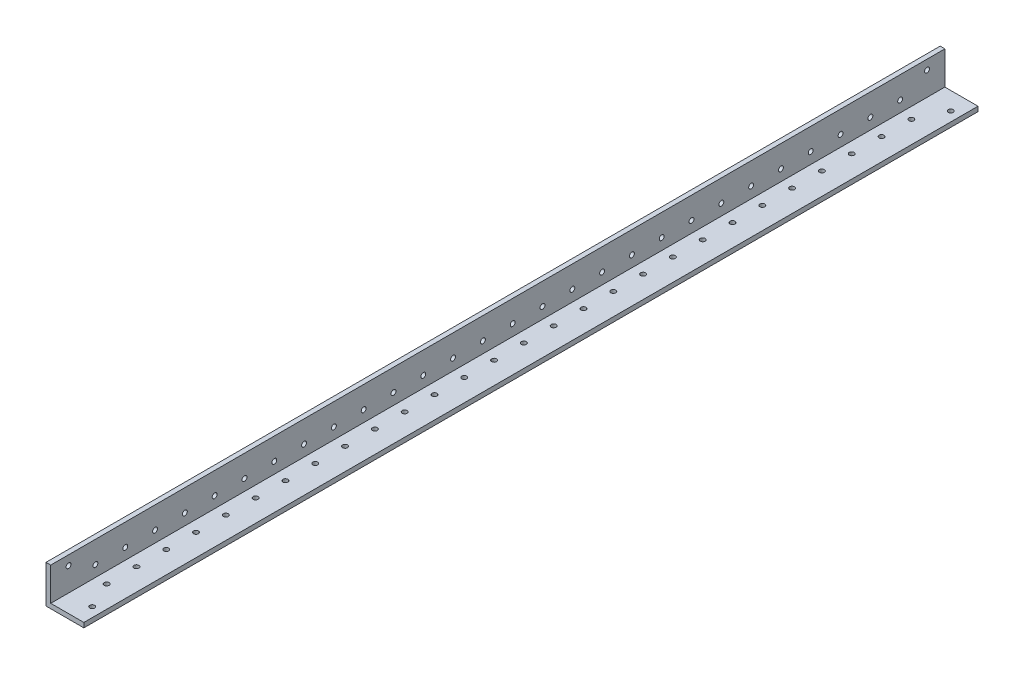
SolidWorks part; units mm, degrees
material "6061-T6 (SS)"
ref_plane "Front Plane" through (0, 0, 0) normal (0, 0, 1) x (1, 0, 0)
ref_plane "Top Plane" through (0, 0, 0) normal (0, 1, 0) x (1, 0, 0)
ref_plane "Right Plane" through (0, 0, 0) normal (1, 0, 0) x (0, 0, -1)
sketch "Sketch1" plane through (0, 0, 0) normal (0, 0, 1) x (1, 0, 0)
  line L0 (0, 25.4) -> (0, 0) construction
  line L1 (0, 0) -> (25.4, 0) construction
  line L2 (25.4, 0) -> (25.4, 3.175) construction
  line L3 (25.4, 3.175) -> (3.175, 3.175) construction
  line L4 (3.175, 3.175) -> (3.175, 25.4) construction
  line L6 (3.175, 25.4) -> (0, 25.4) construction
  arc A0 (3.175, 3.5814) -> (3.5814, 3.175) centre (3.5814, 3.5814) ccw construction
  point P4 (0, 0)
  dimension "Inside Corner Radius" = 0.4064
  dimension "Outside Height" = 25.4
  dimension "Inside Height" = 22.225
  dimension "Outside Width" = 25.4
  dimension "Inside Width" = 22.225
  dimension "Wall Thickness" = 3.175
  dimension "Shape" = 90
sketch "Sketch2" plane through (0, 0, 0) normal (1, 0, 0) x (0, 0, -1)
  line L0 (1219.2, 0) -> (-1219.2, 0) construction
  line L1 (-1219.2, 25.4) -> (-1219.2, 0) construction
  line L2 (1219.2, 25.4) -> (1219.2, 0) construction
  point P0 (-1189.99, 0)
  point P4 (0, 0)
  point P6 (1189.99, 0)
  dimension "D1" = 29.21
  dimension "D2" = 29.21
  dimension "D3" = 25.4
  dimension "Length" = 2438.4
sketch "Sketch3" plane through (0, 0, 0) normal (0, 0, 1) x (1, 0, 0)
  line L0 (3.175, 25.4) -> (0, 25.4)
  line L1 (0, 25.4) -> (0, 0)
  line L2 (0, 0) -> (25.4, 0)
  line L3 (25.4, 0) -> (25.4, 3.175)
  line L4 (25.4, 3.175) -> (3.175, 3.175)
  line L5 (3.175, 3.175) -> (3.175, 25.4)
extrude "Boss-Extrude1" add sketch "Sketch3" along normal mid plane 2438.4
fillet "Fillet1" radius 0.4064 1 edges at (3.175, 3.175, 0)
sketch "Sketch4" plane through (0, 0, 0) normal (-1, 0, 0) x (0, 0, 1)
  line L0 (1219.2, 25.4) -> (1219.2, 0) construction
  line L1 (-1219.2, 25.4) -> (619.2, 25.4)
  line L2 (-1219.2, 25.4) -> (-1219.2, -77.8785)
  line L3 (-1219.2, -77.8785) -> (619.2, -77.8785)
  line L4 (619.2, 25.4) -> (619.2, -77.8785)
  dimension "D1" = 600
extrude "Cut-Extrude1" cut sketch "Sketch4" against normal blind 60
sketch "Sketch5" plane through (0, 0, 619.2) normal (0, 0, -1) x (-1, 0, 0)
  line L0 (-3.175, 3.5814) -> (-3.175, 25.4) construction
  line L1 (-3.175, 5.146) -> (-6.0134, 5.146)
  line L2 (-3.175, 5.146) -> (-3.175, 3.175)
  line L3 (-3.175, 3.175) -> (-6.0134, 3.175)
  line L4 (-6.0134, 5.146) -> (-6.0134, 3.175)
  line L5 (-25.4, 3.175) -> (-3.5814, 3.175) construction
extrude "Cut-Extrude2" cut sketch "Sketch5" against normal blind 700
sketch "Sketch9" plane through (3.175, 0, 0) normal (1, 0, 0) x (0, 0, -1)
  line L0 (-619.2, 3.175) -> (-619.2, 25.4) construction
  line L1 (-1219.2, 3.175) -> (-619.2, 3.175) construction
  line L2 (-1219.2, 3.175) -> (-1219.2, 25.4) construction
  circle A0 centre (-649.2, 10.675) radius 1.65
  circle A1 centre (-669.2, 10.675) radius 1.65
  circle A2 centre (-689.2, 10.675) radius 1.65
  circle A3 centre (-709.2, 10.675) radius 1.65
  circle A4 centre (-729.2, 10.675) radius 1.65
  circle A5 centre (-749.2, 10.675) radius 1.65
  circle A6 centre (-769.2, 10.675) radius 1.65
  circle A7 centre (-789.2, 10.675) radius 1.65
  circle A8 centre (-809.2, 10.675) radius 1.65
  circle A9 centre (-829.2, 10.675) radius 1.65
  circle A10 centre (-849.2, 10.675) radius 1.65
  circle A11 centre (-869.2, 10.675) radius 1.65
  circle A12 centre (-889.2, 10.675) radius 1.65
  circle A13 centre (-909.2, 10.675) radius 1.65
  circle A14 centre (-929.2, 10.675) radius 1.65
  circle A15 centre (-949.2, 10.675) radius 1.65
  circle A16 centre (-969.2, 10.675) radius 1.65
  circle A17 centre (-989.2, 10.675) radius 1.65
  circle A18 centre (-1009.2, 10.675) radius 1.65
  circle A19 centre (-1029.2, 10.675) radius 1.65
  circle A20 centre (-1049.2, 10.675) radius 1.65
  circle A21 centre (-1069.2, 10.675) radius 1.65
  circle A22 centre (-1089.2, 10.675) radius 1.65
  circle A23 centre (-1109.2, 10.675) radius 1.65
  circle A24 centre (-1129.2, 10.675) radius 1.65
  circle A25 centre (-1149.2, 10.675) radius 1.65
  circle A26 centre (-1169.2, 10.675) radius 1.65
  circle A27 centre (-1189.2, 10.675) radius 1.65
  dimension "D1" = 30
  dimension "D2" = 7.5
  dimension "D3" = 3.3
  dimension "D5" = 30
  dimension "D4" = 28
extrude "Cut-Extrude5" cut sketch "Sketch9" against normal blind 20
sketch "Sketch10" plane through (0, 3.175, 0) normal (0, 1, 0) x (1, 0, 0)
  line L0 (25.4, -619.2) -> (3.175, -619.2) construction
  line L1 (3.175, -1219.2) -> (3.175, -619.2) construction
  line L2 (25.4, -1219.2) -> (3.175, -1219.2) construction
  circle A0 centre (10.675, -649.2) radius 1.65
  circle A1 centre (10.675, -669.2) radius 1.65
  circle A2 centre (10.675, -689.2) radius 1.65
  circle A3 centre (10.675, -709.2) radius 1.65
  circle A4 centre (10.675, -729.2) radius 1.65
  circle A5 centre (10.675, -749.2) radius 1.65
  circle A6 centre (10.675, -769.2) radius 1.65
  circle A7 centre (10.675, -789.2) radius 1.65
  circle A8 centre (10.675, -809.2) radius 1.65
  circle A9 centre (10.675, -829.2) radius 1.65
  circle A10 centre (10.675, -849.2) radius 1.65
  circle A11 centre (10.675, -869.2) radius 1.65
  circle A12 centre (10.675, -889.2) radius 1.65
  circle A13 centre (10.675, -909.2) radius 1.65
  circle A14 centre (10.675, -929.2) radius 1.65
  circle A15 centre (10.675, -949.2) radius 1.65
  circle A16 centre (10.675, -969.2) radius 1.65
  circle A17 centre (10.675, -989.2) radius 1.65
  circle A18 centre (10.675, -1009.2) radius 1.65
  circle A19 centre (10.675, -1029.2) radius 1.65
  circle A20 centre (10.675, -1049.2) radius 1.65
  circle A21 centre (10.675, -1069.2) radius 1.65
  circle A22 centre (10.675, -1089.2) radius 1.65
  circle A23 centre (10.675, -1109.2) radius 1.65
  circle A24 centre (10.675, -1129.2) radius 1.65
  circle A25 centre (10.675, -1149.2) radius 1.65
  circle A26 centre (10.675, -1169.2) radius 1.65
  circle A27 centre (10.675, -1189.2) radius 1.65
  dimension "D1" = 30
  dimension "D2" = 7.5
  dimension "D3" = 3.3
  dimension "D5" = 30
  dimension "D4" = 28
extrude "Cut-Extrude6" cut sketch "Sketch10" against normal blind 20
sketch "Sketch11" plane through (0, 3.175, 0) normal (0, 1, 0) x (1, 0, 0)
  circle A0 centre (19.05, -1207.2366) radius 1.65
  circle A1 centre (19.05, -631.1634) radius 1.65
  dimension "D1" = 3.3
extrude "Cut-Extrude7" cut sketch "Sketch11" against normal blind 70
sketch "Sketch12" plane through (3.175, 0, 0) normal (1, 0, 0) x (0, 0, -1)
  circle A0 centre (-1207.2366, 19.05) radius 1.65
  circle A1 centre (-631.1634, 19.05) radius 1.65
  dimension "D1" = 3.3
extrude "Cut-Extrude8" cut sketch "Sketch12" against normal blind 70
equation "\"D1@Boss-Extrude1\"=\"Length@Sketch2\""
equation "\"D1@Sketch2\" = \"Outside Width@Sketch1\" * 1.15"
equation "\"D2@Sketch2\"=\"D1@Sketch2\""
equation "\"D1@Fillet1\"=\"Inside Corner Radius@Sketch1\""
equation "\"D3@Sketch2\"=\"Outside Height@Sketch1\""
